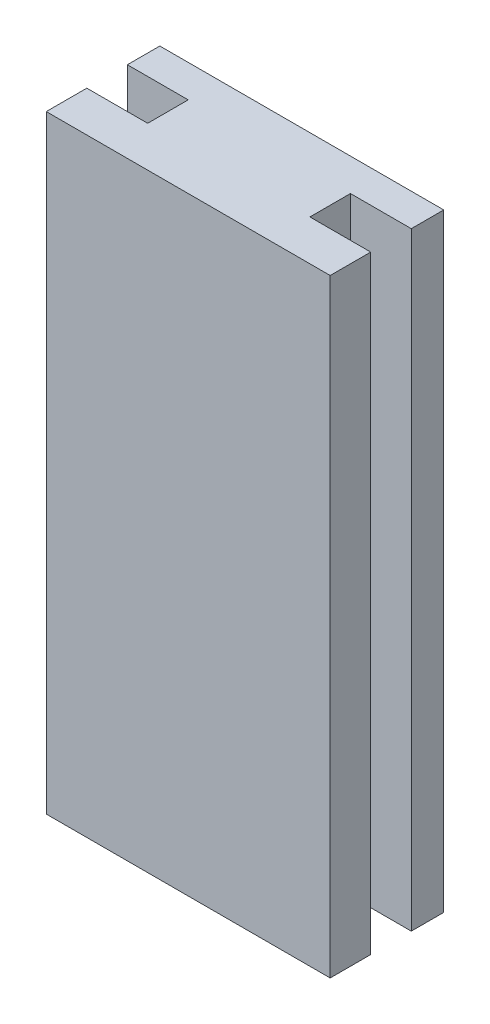
SolidWorks part; units mm, degrees
ref_plane "前视基准面" through (0, 0, 0) normal (0, 0, 1) x (1, 0, 0)
ref_plane "上视基准面" through (0, 0, 0) normal (0, 1, 0) x (1, 0, 0)
ref_plane "右视基准面" through (0, 0, 0) normal (1, 0, 0) x (0, 0, -1)
sketch "草图2" plane through (0, 0, 0) normal (0, 1, 0) x (1, 0, 0)
  line L0 (0, 0) -> (70, 0)
  line L1 (70, 0) -> (70, 10)
  line L2 (70, 10) -> (55, 10)
  line L3 (0, 10) -> (0, 0)
  line L5 (55, 10) -> (55, 20)
  line L6 (55, 20) -> (70, 20)
  line L7 (70, 20) -> (70, 28)
  line L8 (70, 28) -> (0, 28)
  line L9 (0, 28) -> (0, 20)
  line L10 (0, 20) -> (15, 20)
  line L11 (15, 20) -> (15, 10)
  line L12 (15, 10) -> (0, 10)
  point P8 (35, 10)
extrude "凸台-拉伸1" add sketch "草图2" along normal blind 150
